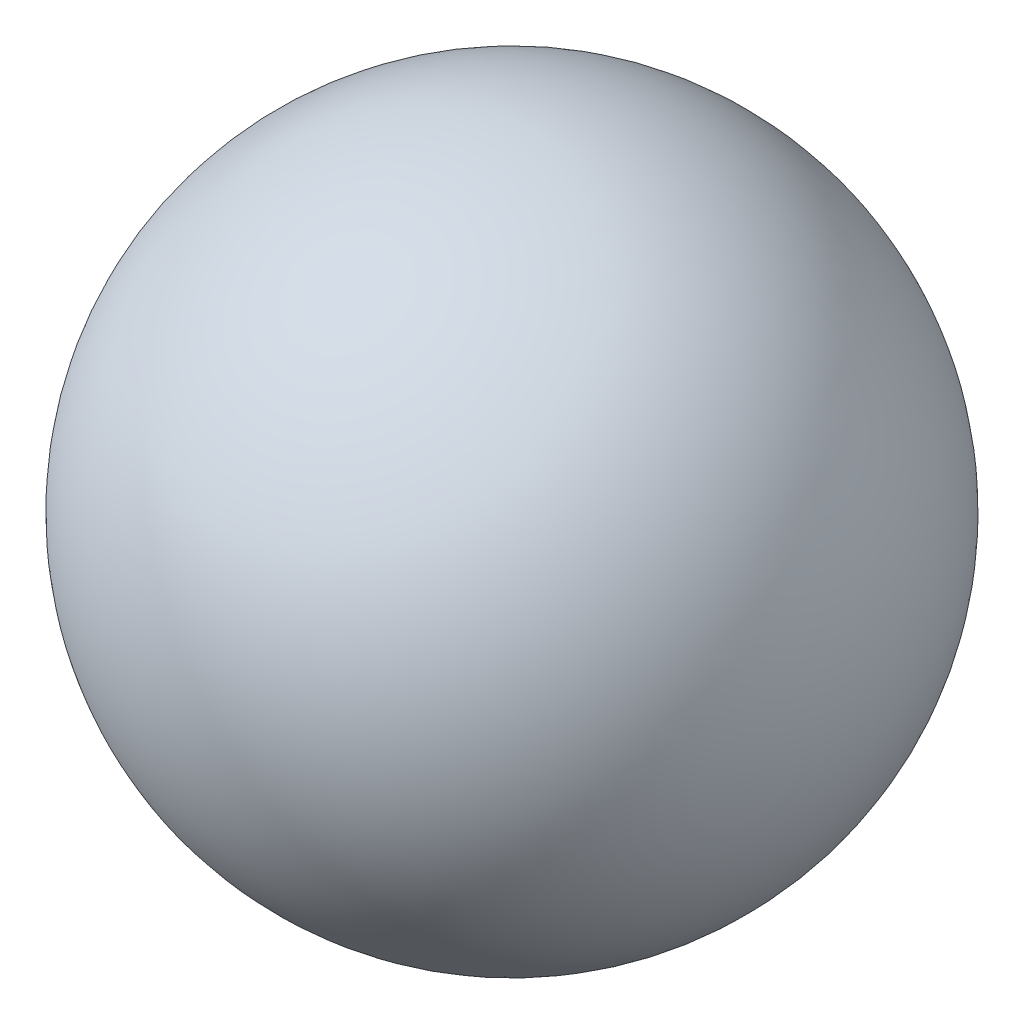
SolidWorks part; units mm, degrees
ref_plane "Front Plane" through (0, 0, 0) normal (0, 0, 1) x (1, 0, 0)
ref_plane "Top Plane" through (0, 0, 0) normal (0, 1, 0) x (1, 0, 0)
ref_plane "Right Plane" through (0, 0, 0) normal (1, 0, 0) x (0, 0, -1)
sketch "Sketch1" plane through (0, 0, 0) normal (0, 1, 0) x (1, 0, 0)
  line L0 (0, 20) -> (0, -20)
  circle A0 centre (0, 0) radius 20
revolve "Revolve1" add sketch "Sketch1" angle 360 about L0
